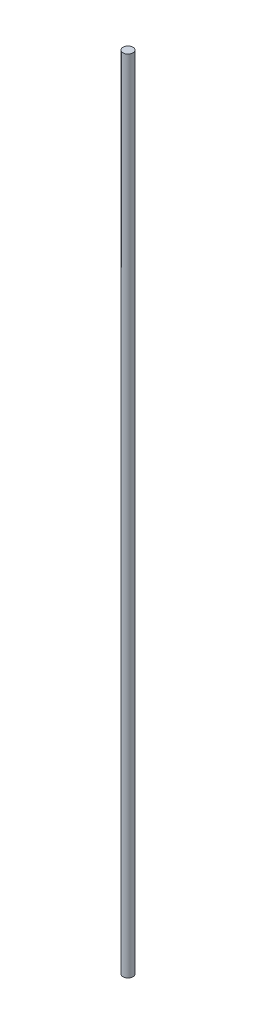
SolidWorks part; units mm, degrees
material "Thornel Mat VMA"
ref_plane "Front Plane" through (0, 0, 0) normal (0, 0, 1) x (1, 0, 0)
ref_plane "Top Plane" through (0, 0, 0) normal (0, 1, 0) x (1, 0, 0)
ref_plane "Right Plane" through (0, 0, 0) normal (1, 0, 0) x (0, 0, -1)
sketch "Sketch1" plane through (0, 0, 0) normal (0, 1, 0) x (1, 0, 0)
  circle A0 centre (0, 0) radius 5.969
  dimension "D1" = 11.938
extrude "Boss-Extrude1" add sketch "Sketch1" along normal mid plane 965.2
